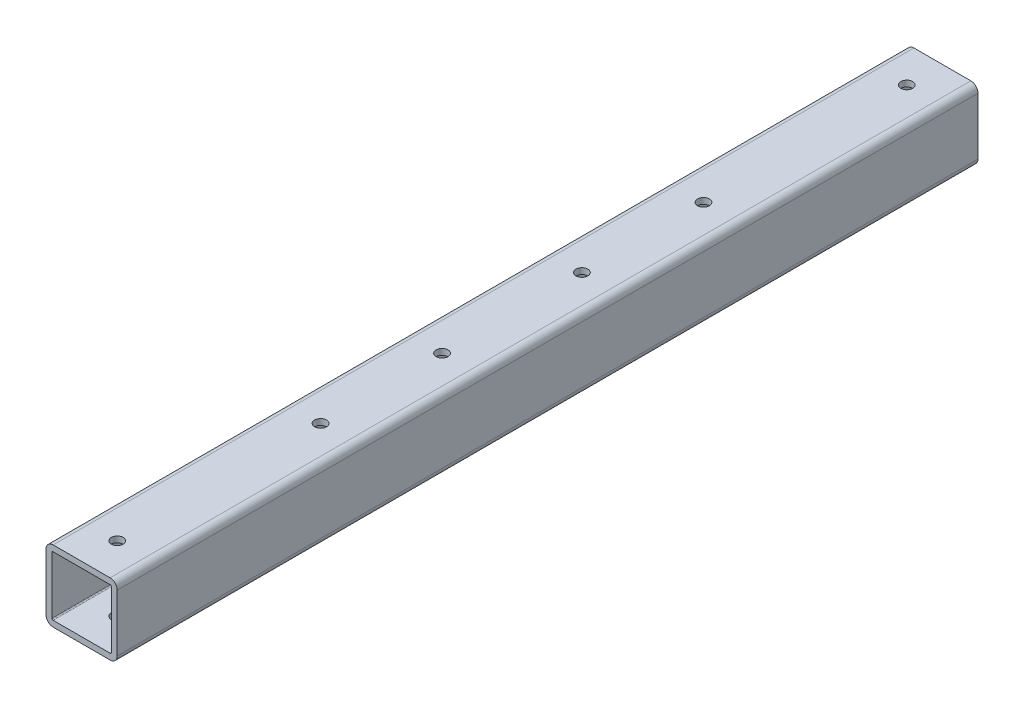
SolidWorks part; units mm, degrees
material "Alloy Steel"
ref_plane "Front Plane" through (0, 0, 0) normal (0, 0, 1) x (1, 0, 0)
ref_plane "Top Plane" through (0, 0, 0) normal (0, 1, 0) x (1, 0, 0)
ref_plane "Right Plane" through (0, 0, 0) normal (1, 0, 0) x (0, 0, -1)
sketch "Sketch1" plane through (0, 0, 0) normal (0, 0, 1) x (1, 0, 0)
  line L0 (-15.875, 15.875) -> (-15.875, -15.875)
  line L1 (-19.05, 19.05) -> (19.05, 19.05)
  line L2 (-19.05, 19.05) -> (-19.05, -19.05)
  line L3 (-19.05, -19.05) -> (19.05, -19.05)
  line L4 (19.05, 19.05) -> (19.05, -19.05)
  line L5 (-19.05, 19.05) -> (19.05, -19.05) construction
  line L6 (-19.05, -19.05) -> (19.05, 19.05) construction
  line L7 (-15.875, -15.875) -> (15.875, -15.875)
  line L8 (15.875, 15.875) -> (15.875, -15.875)
  line L9 (-15.875, 15.875) -> (15.875, 15.875)
  point P0 (0, 0)
  dimension "D2" = 38.1
  dimension "D3" = 38.1
  dimension "D1" = 3.175
extrude "Boss-Extrude1" add sketch "Sketch1" along normal mid plane 460.375
fillet "Fillet1" radius 3.81 4 edges at (19.05, 19.05, 0) (-19.05, 19.05, 0) (-19.05, -19.05, 0) (19.05, -19.05, 0)
fillet "Fillet2" radius 0.635 4 edges at (15.875, -15.875, 0) (-15.875, -15.875, 0) (-15.875, 15.875, 0) (15.875, 15.875, 0)
sketch "Sketch2" plane through (0, 0, 0) normal (0, 1, 0) x (1, 0, 0)
  line L0 (0, -230.1875) -> (0, 230.1875) construction
  line L1 (15.24, -230.1875) -> (-15.24, -230.1875) construction
  line L2 (15.24, 230.1875) -> (-15.24, 230.1875) construction
  circle A0 centre (0, -211.1375) radius 3.175
  circle A1 centre (0, -102.4) radius 3.175
  circle A2 centre (0, -37.4) radius 3.175
  circle A3 centre (0, 37.4) radius 3.175
  circle A4 centre (0, 102.4) radius 3.175
  circle A5 centre (0, 211.1375) radius 3.175
  dimension "D1" = 6.35
  dimension "D2" = 19.05
  dimension "D3" = 127.7875
  dimension "D4" = 192.7875
  dimension "D5" = 267.5875
  dimension "D6" = 332.5875
  dimension "D7" = 19.05
extrude "Cut-Extrude1" cut sketch "Sketch2" against normal through all both and the other way through all
